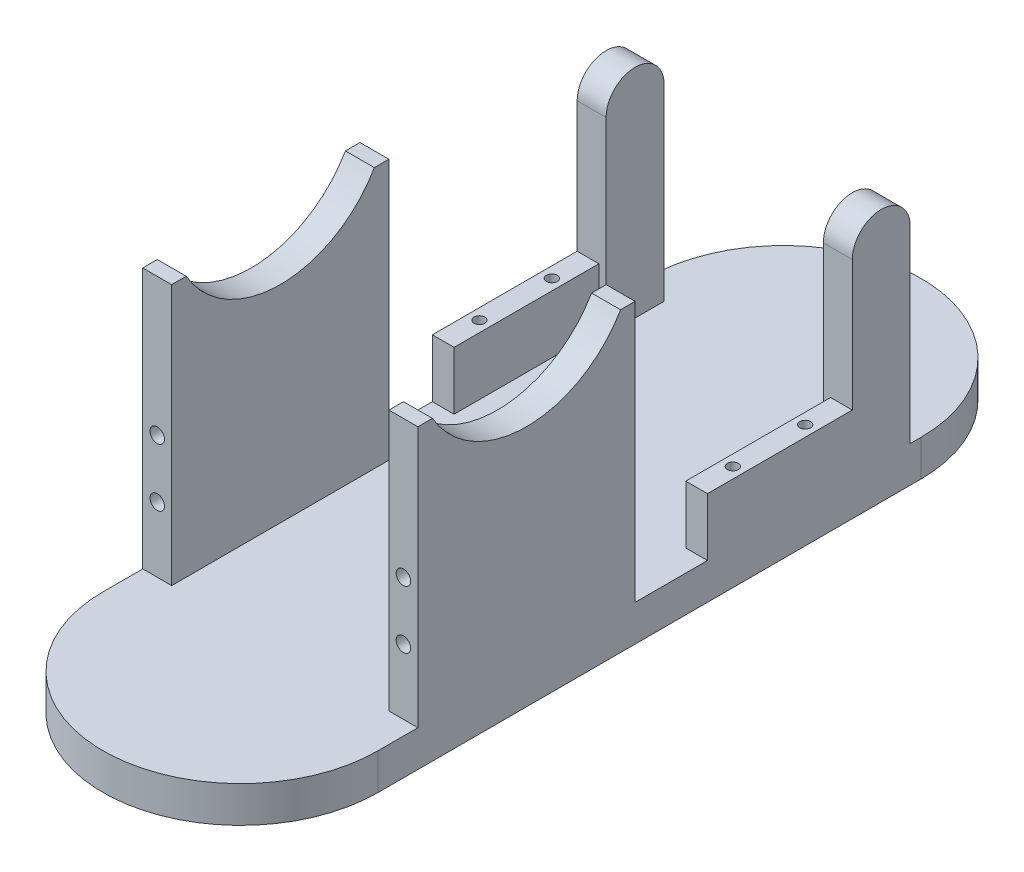
SolidWorks part; units mm, degrees
ref_plane "Front" through (0, 0, 0) normal (0, 0, 1) x (1, 0, 0)
ref_plane "Top" through (0, 0, 0) normal (0, 1, 0) x (1, 0, 0)
ref_plane "Right" through (0, 0, 0) normal (1, 0, 0) x (0, 0, -1)
sketch "草图1" plane through (0, 0, 0) normal (0, 1, 0) x (1, 0, 0)
  line L0 (0, 24.0367) -> (0, 0) construction
  line L1 (0, 0) -> (-31.1152, 0) construction
  line L2 (0, -75) -> (0, 75) construction
  line L3 (-38, -75) -> (-38, 75)
  line L4 (38, -75) -> (38, 75)
  arc A0 (-38, -75) -> (38, -75) centre (0, -75) ccw
  arc A1 (38, 75) -> (-38, 75) centre (0, 75) ccw
  point P6 (0, 0)
extrude "凸台-拉伸1" add sketch "草图1" along normal blind 10
sketch "草图3" plane through (0, 10, 0) normal (0, 1, 0) x (1, 0, 0)
  line L0 (-87.6038, -64) -> (61.1928, -64) construction
  line L1 (-38, 75) -> (-38, -75) construction
  line L2 (-38, -64) -> (-30, -64)
  line L3 (-38, -64) -> (-38, -4)
  line L4 (-38, -4) -> (-30, -4)
  line L5 (-30, -64) -> (-30, -4)
  line L6 (38, -75) -> (38, 75) construction
  line L7 (38, -64) -> (30, -64)
  line L8 (38, -64) -> (38, -4)
  line L9 (38, -4) -> (30, -4)
  line L10 (30, -64) -> (30, -4)
  dimension "D1" = 64
  dimension "D2" = 60
  dimension "D3" = 8
  dimension "D4" = 8
  dimension "D5" = 60
extrude "凸台-拉伸2" add sketch "草图3" along normal blind 72
sketch "草图4" plane through (0, 10, 0) normal (0, 1, 0) x (1, 0, 0)
  line L0 (-57.3538, 16) -> (64.3655, 16) construction
  line L1 (-38, 75) -> (-38, -4) construction
  line L2 (-38, 16) -> (-32, 16)
  line L3 (-38, 16) -> (-38, 56)
  line L4 (-38, 56) -> (-32, 56)
  line L5 (-32, 16) -> (-32, 56)
  line L6 (38, -4) -> (38, 75) construction
  line L7 (38, 16) -> (32, 16)
  line L8 (38, 16) -> (38, 56)
  line L9 (38, 56) -> (32, 56)
  line L10 (32, 16) -> (32, 56)
  dimension "D1" = 16
  dimension "D2" = 6
  dimension "D3" = 40
  dimension "D4" = 6
extrude "凸台-拉伸3" add sketch "草图4" along normal blind 16
sketch "草图5" plane through (38, 0, 0) normal (1, 0, 0) x (0, 0, -1)
  line L0 (-64, 82) -> (-4, 82) construction
  circle A0 centre (-34, 97) radius 30
  dimension "D1" = 15
extrude "切除-拉伸1" cut sketch "草图5" against normal through all
sketch "草图6" plane through (0, 0, 64) normal (0, 0, 1) x (1, 0, 0)
  line L0 (-49.7987, 44) -> (50.3023, 44) construction
  line L1 (-49.7987, 28) -> (51.0857, 28) construction
  line L2 (-38, 0) -> (38, 0) construction
  circle A0 centre (-34, 44) radius 2
  circle A1 centre (-34, 28) radius 2
  circle A2 centre (34, 44) radius 2
  circle A3 centre (34, 28) radius 2
  dimension "D1" = 44
  dimension "D2" = 28
extrude "切除-拉伸2" cut sketch "草图6" against normal blind 10
sketch "草图7" plane through (0, 26, 0) normal (0, 1, 0) x (1, 0, 0)
  line L0 (-38, 36) -> (38, 36) construction
  line L1 (-38, 56) -> (-38, 16) construction
  line L2 (38, 16) -> (38, 56) construction
  line L3 (-32, 16) -> (-32, 56) construction
  line L4 (-38, 16) -> (-32, 16) construction
  line L5 (35, 16) -> (35, 56) construction
  line L6 (32, 16) -> (38, 16) construction
  line L7 (38, 56) -> (32, 56) construction
  circle A0 centre (-35, 26) radius 1.5
  circle A1 centre (-35, 46) radius 1.5
  circle A2 centre (35, 26) radius 1.5
  circle A3 centre (35, 46) radius 1.5
  point P6 (-32, 36)
  dimension "D2" = 20
  dimension "D1" = 10
extrude "切除-拉伸3" cut sketch "草图7" against normal blind 10
sketch "草图8" plane through (0, 10, 0) normal (0, 1, 0) x (1, 0, 0)
  line L1 (-38, 56) -> (-30, 56)
  line L2 (-38, 56) -> (-38, 72)
  line L3 (-38, 72) -> (-30, 72)
  line L4 (-30, 56) -> (-30, 72)
  line L5 (38, 56) -> (30, 56)
  line L6 (38, 56) -> (38, 72)
  line L7 (38, 72) -> (30, 72)
  line L8 (30, 56) -> (30, 72)
  dimension "D1" = 16
  dimension "D2" = 8
  dimension "D3" = 16
  dimension "D4" = 8
extrude "凸台-拉伸4" add sketch "草图8" along normal blind 60
sketch "草图9" plane through (38, 0, 0) normal (1, 0, 0) x (0, 0, -1)
  line L0 (56, 70) -> (72, 70) construction
  line L2 (56, 62) -> (56, 75)
  line L3 (56, 75) -> (72, 75)
  line L4 (72, 62) -> (72, 75)
  arc A0 (72, 62) -> (56, 62) centre (64, 62) ccw
  dimension "D1" = 8
  dimension "D2" = 5
extrude "切除-拉伸4" cut sketch "草图9" against normal through all
